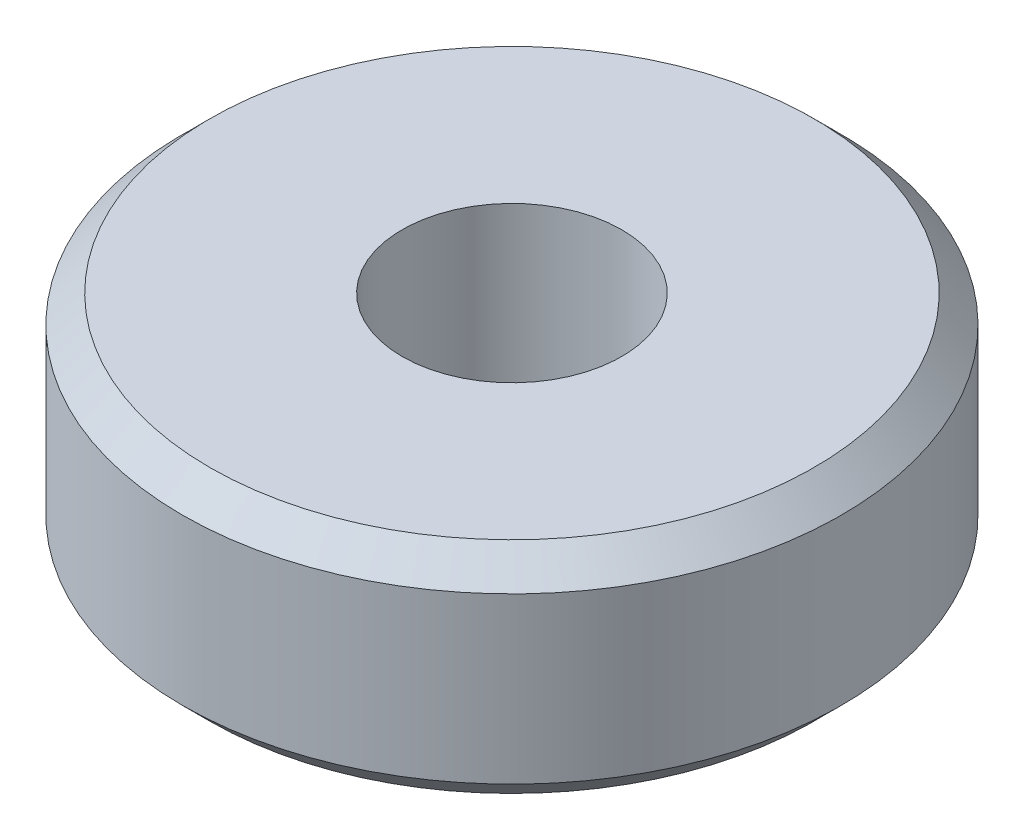
SolidWorks part; units mm, degrees
ref_plane "Front Plane" through (0, 0, 0) normal (0, 0, 1) x (1, 0, 0)
ref_plane "Top Plane" through (0, 0, 0) normal (0, 1, 0) x (1, 0, 0)
ref_plane "Right Plane" through (0, 0, 0) normal (1, 0, 0) x (0, 0, -1)
sketch "Sketch1" plane through (0, 0, 0) normal (0, 1, 0) x (1, 0, 0)
  circle A0 centre (0, 0) radius 6
  circle A1 centre (0, 0) radius 2
  dimension "D1" = 4
  dimension "D2" = 12
extrude "Boss-Extrude1" add sketch "Sketch1" along normal blind 4
chamfer "Chamfer1" distance 0.5 angle 45 2 edges at (0, 4, 6) (0, 0, 6)
